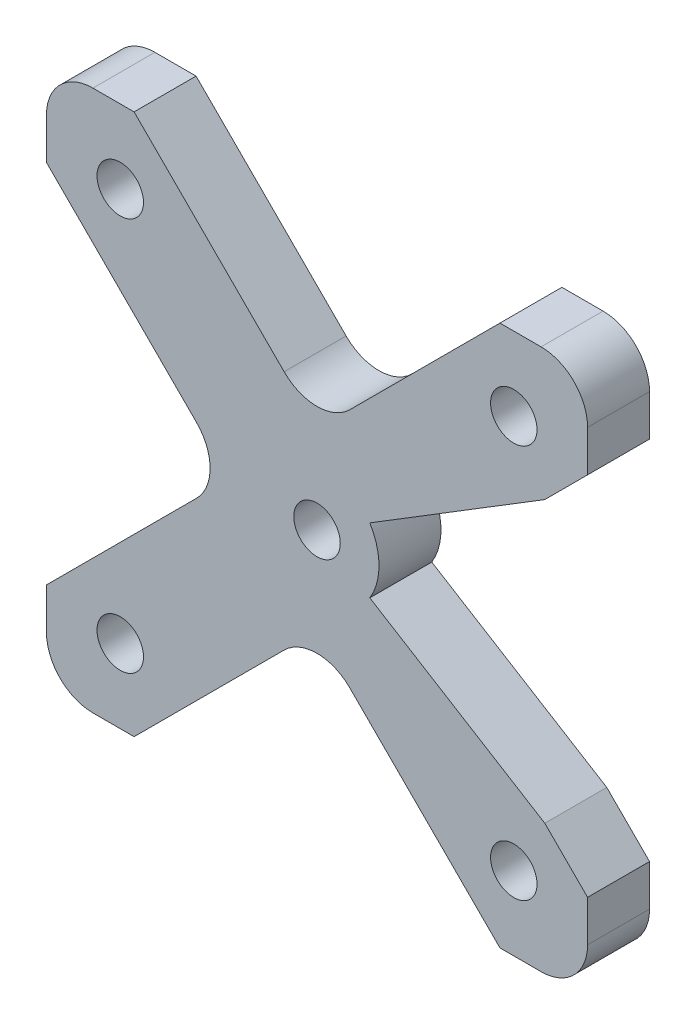
SolidWorks part; units mm, degrees
ref_plane "Front Plane" through (0, 0, 0) normal (0, 0, 1) x (1, 0, 0)
ref_plane "Top Plane" through (0, 0, 0) normal (0, 1, 0) x (1, 0, 0)
ref_plane "Right Plane" through (0, 0, 0) normal (1, 0, 0) x (0, 0, -1)
sketch "Sketch1" plane through (0, 0, 0) normal (0, 0, 1) x (1, 0, 0)
  line L1 (17.4625, -17.4625) -> (-17.4625, -17.4625)
  line L2 (17.4625, -17.4625) -> (17.4625, 17.4625)
  line L3 (17.4625, 17.4625) -> (-17.4625, 17.4625)
  line L4 (-17.4625, -17.4625) -> (-17.4625, 17.4625)
  line L5 (17.4625, -17.4625) -> (-17.4625, 17.4625) construction
  line L6 (17.4625, 17.4625) -> (-17.4625, -17.4625) construction
  line L7 (12.7, -12.7) -> (-12.7, -12.7)
  line L8 (12.7, -12.7) -> (12.7, 12.7)
  line L9 (12.7, 12.7) -> (-12.7, 12.7)
  line L10 (-12.7, -12.7) -> (-12.7, 12.7)
  line L11 (12.7, -12.7) -> (-12.7, 12.7) construction
  line L12 (12.7, 12.7) -> (-12.7, -12.7) construction
  circle A0 centre (-12.7, 12.7) radius 1.5
  circle A1 centre (12.7, 12.7) radius 1.5
  circle A2 centre (-12.7, -12.7) radius 1.5
  circle A3 centre (12.7, -12.7) radius 1.5
  circle A4 centre (0, 0) radius 1.5
  point P0 (0, 0)
  point P6 (0, 0)
  dimension "D4" = 3
  dimension "D5" = 3
  dimension "D1" = 34.925
  dimension "D2" = 34.925
  dimension "D3" = 25.4
extrude "Boss-Extrude1" add sketch "Sketch1" along normal blind 4 contours L4 L1 L2 L3 A3 L7 A2 L10 A0 L9 A1 L8 | A3 L8 A1 L9 A0 L10 A2 L7
sketch "Sketch2" plane through (0, 0, 4) normal (0, 0, 1) x (1, 0, 0)
  line L0 (-17.4625, 17.4625) -> (17.4625, -17.4625) construction
  line L1 (-20.2909, 14.6341) -> (14.6341, -20.2909)
  line L2 (-14.6341, 20.2909) -> (20.2909, -14.6341)
  line L3 (-17.4625, -17.4625) -> (17.4625, 17.4625) construction
  line L4 (-14.6341, -20.2909) -> (20.2909, 14.6341)
  line L5 (-20.2909, -14.6341) -> (14.6341, 20.2909)
  line L10 (-17.4625, 17.4625) -> (-17.4625, -17.4625)
  line L11 (-17.4625, -17.4625) -> (17.4625, -17.4625)
  line L12 (17.4625, -17.4625) -> (17.4625, 17.4625)
  line L13 (17.4625, 17.4625) -> (-17.4625, 17.4625)
  line L14 (-17.4625, 17.4625) -> (-17.4625, -17.4625)
  line L15 (-17.4625, -17.4625) -> (17.4625, -17.4625)
  line L16 (17.4625, -17.4625) -> (17.4625, 17.4625)
  line L17 (17.4625, 17.4625) -> (-17.4625, 17.4625)
  line M11 (-17.4625, 17.4625) -> (-17.4625, -17.4625)
  line M12 (-17.4625, -17.4625) -> (17.4625, -17.4625)
  line M13 (17.4625, -17.4625) -> (17.4625, 17.4625)
  line M14 (17.4625, 17.4625) -> (-17.4625, 17.4625)
  dimension "D1" = 4
  dimension "D2" = 4
  dimension "D3" = 4
  dimension "D4" = 4
  dimension "D5" = 0
extrude "Cut-Extrude1" cut sketch "Sketch2" against normal blind 5.08 contours L5 L1 M11 | L2 L5 M14 | L4 L2 M13 | L4 L1 M12
fillet "Fillet1" radius 3 8 edges at (5.6569, 0, 2) (-5.6569, 0, 2) (0, -5.6569, 2) (-17.4625, -17.4625, 2) (17.4625, -17.4625, 2) (17.4625, 17.4625, 2) (0, 5.6569, 2) (-17.4625, 17.4625, 2)
sketch "Sketch3" plane through (0, 0, 0) normal (0, 0, -1) x (-1, 0, 0)
  line L0 (-7.7782, -2.1213) -> (-17.4625, -11.8056) construction
  line L1 (-7.7782, 2.1213) -> (-17.4625, 11.8056) construction
  line L2 (0, 0) -> (-14.7, -9.0431)
  line L4 (-14.7, 9.0431) -> (0, 0)
  circle A0 centre (0, 0) radius 4
  circle A1 centre (-12.7, 12.7) radius 1.5 construction
  line M21 (-17.4625, 11.8056) -> (-7.7782, 2.1213)
  arc M22 (-7.7782, 2.1213) -> (-7.7782, -2.1213) centre (-9.8995, 0) cw
  line M23 (-7.7782, -2.1213) -> (-17.4625, -11.8056)
  dimension "D1" = 8
  dimension "D2" = 0
  dimension "D3" = 2
extrude "Cut-Extrude2" cut sketch "Sketch3" against normal blind 5.08 contours A0 L4 L2 M21 M22 M23
